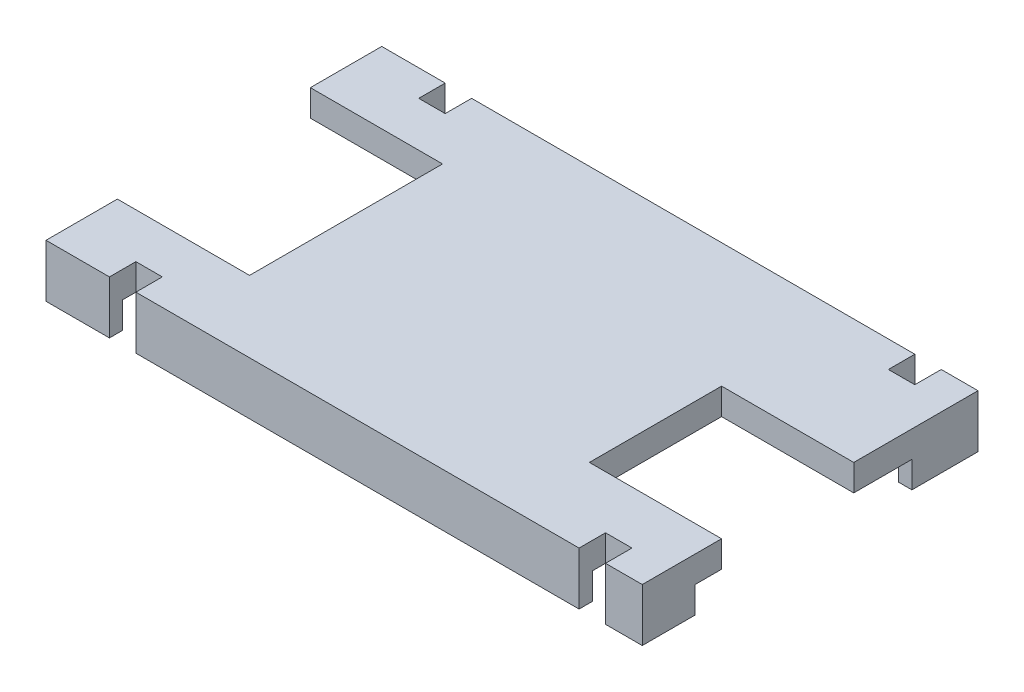
SolidWorks part; units mm, degrees
ref_plane "Front Plane" through (0, 0, 0) normal (0, 0, 1) x (1, 0, 0)
ref_plane "Top Plane" through (0, 0, 0) normal (0, 1, 0) x (1, 0, 0)
ref_plane "Right Plane" through (0, 0, 0) normal (1, 0, 0) x (0, 0, -1)
sketch "Sketch1" plane through (0, 0, 0) normal (0, 1, 0) x (1, 0, 0)
  line L1 (-40.0407, 20.9565) -> (-17.4855, 20.9565)
  line L2 (-40.0407, 20.9565) -> (-40.0407, 8.2565)
  line L3 (-40.0407, 8.2565) -> (-17.4855, 8.2565)
  line L4 (-17.4855, 20.9565) -> (-17.4855, 8.2565)
  dimension "D1" = 22.5552
  dimension "D2" = 12.7
extrude "Boss-Extrude1" add sketch "Sketch1" along normal blind 1
sketch "Sketch2" plane through (0, 1, 0) normal (0, 1, 0) x (1, 0, 0)
  line L0 (-17.4855, 20.9565) -> (-40.0407, 20.9565) construction
  line L1 (-40.0407, 18.2565) -> (-35.0407, 18.2565)
  line L2 (-40.0407, 18.2565) -> (-40.0407, 10.9565)
  line L3 (-40.0407, 10.9565) -> (-35.0407, 10.9565)
  line L4 (-35.0407, 18.2565) -> (-35.0407, 10.9565)
  line L7 (-40.0407, 20.9565) -> (-40.0407, 8.2565) construction
  dimension "D1" = 7.3
  dimension "D2" = 5
  dimension "D3" = 2.7
  dimension "D4" = 0
extrude "Cut-Extrude1" cut sketch "Sketch2" against normal blind 1
sketch "Sketch3" plane through (0, 1, 0) normal (0, 1, 0) x (1, 0, 0)
  line L0 (-17.4855, 8.2565) -> (-17.4855, 20.9565) construction
  line L1 (-17.4855, 16.2565) -> (-22.4855, 16.2565)
  line L2 (-17.4855, 16.2565) -> (-17.4855, 11.2565)
  line L3 (-17.4855, 11.2565) -> (-22.4855, 11.2565)
  line L4 (-22.4855, 16.2565) -> (-22.4855, 11.2565)
  line L5 (-40.0407, 8.2565) -> (-17.4855, 8.2565) construction
  line L6 (-17.4855, 20.9565) -> (-40.0407, 20.9565) construction
  dimension "D1" = 5
  dimension "D2" = 3
  dimension "D3" = 4.7
  dimension "D4" = 5
extrude "Cut-Extrude2" cut sketch "Sketch3" against normal blind 1
sketch "Sketch4" plane through (0, 0, 0) normal (0, -1, 0) x (1, 0, 0)
  line L0 (-17.4855, -8.2565) -> (-17.4855, -11.2565) construction
  line L1 (-40.0407, -8.2565) -> (-17.4855, -8.2565)
  line L2 (-40.0407, -8.2565) -> (-40.0407, -8.7565)
  line L3 (-40.0407, -8.7565) -> (-17.4855, -8.7565)
  line L4 (-17.4855, -8.2565) -> (-17.4855, -8.7565)
  line L5 (-40.0407, -20.9565) -> (-40.0407, -18.2565) construction
  line L6 (-17.4855, -8.2565) -> (-17.9855, -8.2565)
  line L7 (-17.4855, -8.2565) -> (-17.4855, -10.2565)
  line L8 (-17.4855, -10.2565) -> (-17.9855, -10.2565)
  line L9 (-17.9855, -8.2565) -> (-17.9855, -10.2565)
  line L10 (-40.0407, -20.4565) -> (-17.4855, -20.4565)
  line L11 (-40.0407, -20.4565) -> (-40.0407, -20.9565)
  line L12 (-40.0407, -20.9565) -> (-17.4855, -20.9565)
  line L13 (-17.4855, -20.4565) -> (-17.4855, -20.9565)
  line L15 (-17.4855, -20.9565) -> (-17.9855, -20.9565)
  line L16 (-17.4855, -20.9565) -> (-17.4855, -18.4565)
  line L17 (-17.4855, -18.4565) -> (-17.9855, -18.4565)
  line L18 (-17.9855, -20.9565) -> (-17.9855, -18.4565)
  line M3 (-17.4855, -11.2565) -> (-17.4855, -8.2565)
  line M5 (-40.0407, -8.2565) -> (-40.0407, -10.9565)
  line M9 (-40.0407, -18.2565) -> (-40.0407, -20.9565)
  line M10 (-40.0407, -20.9565) -> (-17.4855, -20.9565)
  line M11 (-17.4855, -20.9565) -> (-17.4855, -16.2565)
  dimension "D1" = 0.5
  dimension "D2" = 0.5
  dimension "D3" = 2
  dimension "D4" = 0.5
  dimension "D5" = 2.5
extrude "Boss-Extrude2" add sketch "Sketch4" along normal blind 1 contours L9 L1 L3 M5 | L3 L9 L8 M3 | L18 L10 L17 M11 | L18 L12 L10 M11 | L18 L10 M10 M9
sketch "Sketch7" plane through (0, 1, 0) normal (0, 1, 0) x (1, 0, 0)
  line L0 (-17.4855, 20.9565) -> (-40.0407, 20.9565) construction
  line L1 (-37.6407, 20.9565) -> (-36.6407, 20.9565)
  line L2 (-37.6407, 20.9565) -> (-37.6407, 19.9565)
  line L3 (-37.6407, 19.9565) -> (-36.6407, 19.9565)
  line L4 (-36.6407, 20.9565) -> (-36.6407, 19.9565)
  line L5 (-40.0407, 20.9565) -> (-40.0407, 18.2565) construction
  line L6 (-37.6407, 9.2565) -> (-37.6407, 8.2565)
  line L7 (-37.6407, 9.2565) -> (-36.6407, 9.2565)
  line L8 (-36.6407, 9.2565) -> (-36.6407, 8.2565)
  line L9 (-37.6407, 8.2565) -> (-36.6407, 8.2565)
  line L10 (-17.4855, 16.2565) -> (-17.4855, 20.9565) construction
  line L11 (-18.8755, 20.9565) -> (-19.8755, 20.9565)
  line L12 (-18.8755, 20.9565) -> (-18.8755, 19.9565)
  line L13 (-18.8755, 19.9565) -> (-19.8755, 19.9565)
  line L14 (-19.8755, 20.9565) -> (-19.8755, 19.9565)
  line L15 (-19.8755, 9.2565) -> (-19.8755, 8.2565)
  line L16 (-18.8755, 9.2565) -> (-19.8755, 9.2565)
  line L17 (-18.8755, 9.2565) -> (-18.8755, 8.2565)
  line L18 (-18.8755, 8.2565) -> (-19.8755, 8.2565)
  dimension "D1" = 1
  dimension "D2" = 1
  dimension "D3" = 2.4
  dimension "D5" = 1
  dimension "D6" = 1
  dimension "D7" = 1.39
  dimension "D4" = 2
  dimension "D8" = 2
extrude "Cut-Extrude3" cut sketch "Sketch7" against normal blind 3
sketch "Sketch8" plane through (0, 1, 0) normal (0, 1, 0) x (1, 0, 0)
  line L0 (-19.8755, 20.9565) -> (-36.6407, 20.9565) construction
  line L1 (-36.6407, 8.2565) -> (-19.8755, 8.2565) construction
  point P0 (-35.0407, 20.9565)
  point P1 (-22.4855, 20.9565)
  point P4 (-22.4855, 8.2565)
  point P5 (-35.0407, 8.2565)
